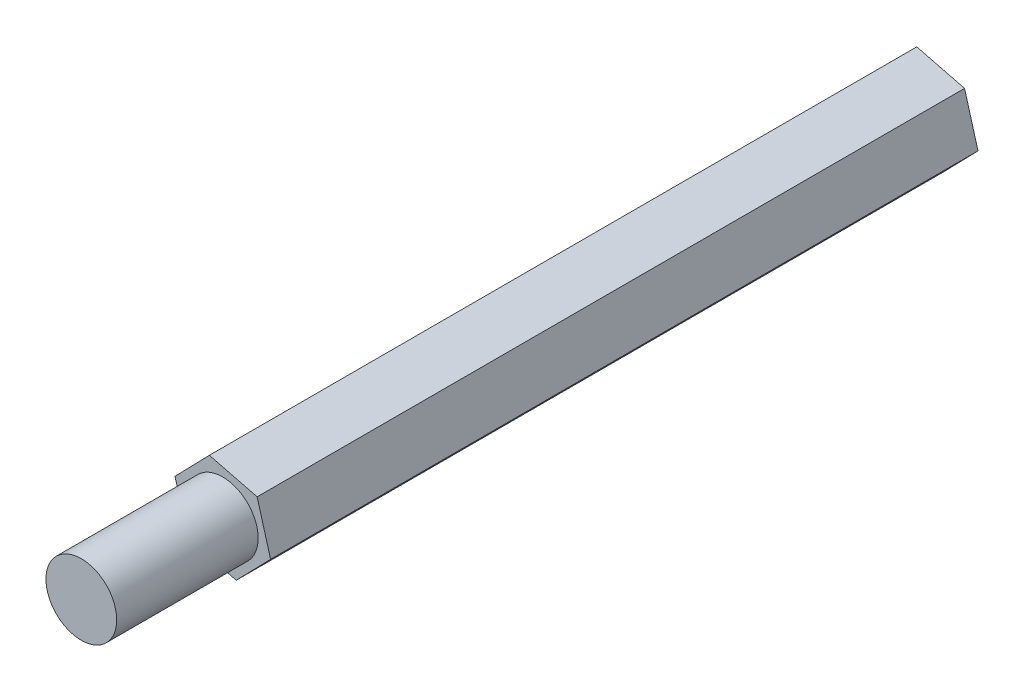
SolidWorks part; units mm, degrees
ref_plane "前视基准面" through (0, 0, 0) normal (0, 0, 1) x (1, 0, 0)
ref_plane "上视基准面" through (0, 0, 0) normal (0, 1, 0) x (1, 0, 0)
ref_plane "右视基准面" through (0, 0, 0) normal (1, 0, 0) x (0, 0, -1)
sketch "草图1" plane through (0, 0, 0) normal (0, 0, 1) x (1, 0, 0)
  circle A0 centre (0, 0) radius 1.5
extrude "凸台-拉伸1" add sketch "草图1" along normal blind 6
sketch "草图2" plane through (0, 0, 0) normal (0, 0, -1) x (-1, 0, 0)
  line L1 (1.4563, -1.4992) -> (2.0265, 0.5116)
  line L2 (2.0265, 0.5116) -> (0.5702, 2.0108)
  line L3 (0.5702, 2.0108) -> (-1.4563, 1.4992)
  line L4 (-1.4563, 1.4992) -> (-2.0265, -0.5116)
  line L5 (-2.0265, -0.5116) -> (-0.5702, -2.0108)
  line L6 (-0.5702, -2.0108) -> (1.4563, -1.4992)
  circle A0 centre (0, 0) radius 1.8101 construction
extrude "凸台-拉伸2" add sketch "草图2" along normal blind 30
